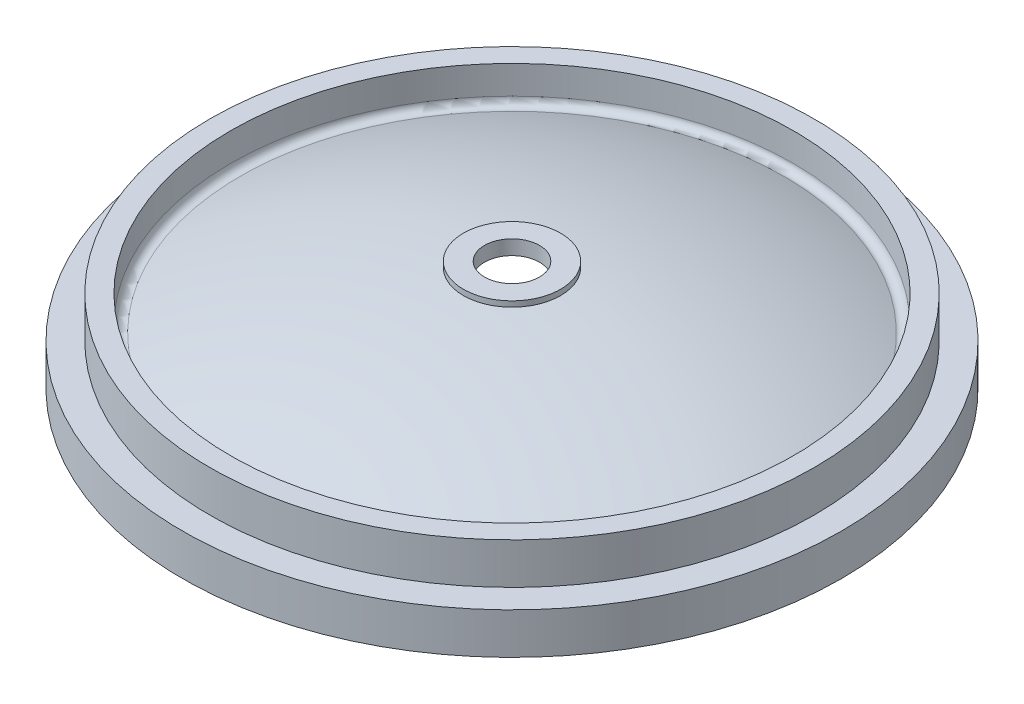
SolidWorks part; units mm, degrees
material "6061-T6 (SS)"
ref_plane "Front Plane" through (0, 0, 0) normal (0, 0, 1) x (1, 0, 0)
ref_plane "Top Plane" through (0, 0, 0) normal (0, 1, 0) x (1, 0, 0)
ref_plane "Right Plane" through (0, 0, 0) normal (1, 0, 0) x (0, 0, -1)
sketch "Sketch1" plane through (0, 0, 0) normal (0, 0, 1) x (1, 0, 0)
  line L0 (0, 50.9225) -> (0, 44.45)
  line L1 (152.4, 19.05) -> (152.4, 0)
  line L2 (152.4, 0) -> (147.6375, 0)
  line L3 (147.6375, 0) -> (147.6375, 4.3928)
  line L4 (152.4, 19.05) -> (139.7, 19.05)
  line L5 (139.7, 19.05) -> (139.7, 38.1)
  line L6 (139.7, 38.1) -> (130.175, 38.1)
  line L7 (130.175, 38.1) -> (130.175, 20.0164)
  line L8 (22.479, 50.9225) -> (0, 50.9225)
  line L9 (22.479, 50.9225) -> (22.479, 48.3825)
  arc A0 (130.175, 20.0164) -> (22.479, 48.3825) centre (0, -255.5875) ccw
  arc A1 (147.6375, 4.3928) -> (0, 44.45) centre (0, -247.65) ccw
  point P10 (150.0188, 0)
  point P13 (22.479, 48.3825)
  point P17 (0, 0)
  point P18 (0, 0)
  point P19 (0, 0)
  point P20 (0, 0)
  point P21 (0, 0)
  dimension "D4" = 19.05
  dimension "D5" = 4.7625
  dimension "D1" = 304.8
  dimension "D7" = 9.525
  dimension "D9" = 292.1
  dimension "D10" = 19.05
  dimension "D12" = 7.9375
  dimension "D2" = 152.4
  dimension "D3" = 25.4
  dimension "D6" = 12.7
  dimension "D8" = 2.54
  dimension "D11" = 22.479
revolve "Revolve1" add sketch "Sketch1" angle 360 about L0
ref_plane "Plane1" through (0, 49.2125, 0) normal (0, 1, 0) x (1, 0, 0)
fillet "Fillet1" radius 3.175 1 edges at (-130.175, 20.0164, 0)
hole_wizard "Hole1" positions "Sketch3" profile "Sketch4" legacy
sketch "Sketch3" plane through (0, 50.9225, 0) normal (0, 1, 0) x (1, 0, 0)
  point P0 (0, 0)
sketch "Sketch4" plane through (0, 50.9225, 0) normal (1, 0, 0) x (0, 0, 1)
  line L0 (0, 0) -> (0, 6.4725)
  line L1 (0, 6.4725) -> (12.7, 6.4725)
  line L2 (12.7, 6.4725) -> (12.7, 0)
  line L3 (12.7, 0) -> (0, 0)
  line L4 (0, 110) -> (0, -10) construction
  dimension "Diameter" = 25.4
  dimension "Depth" = 6.4725
